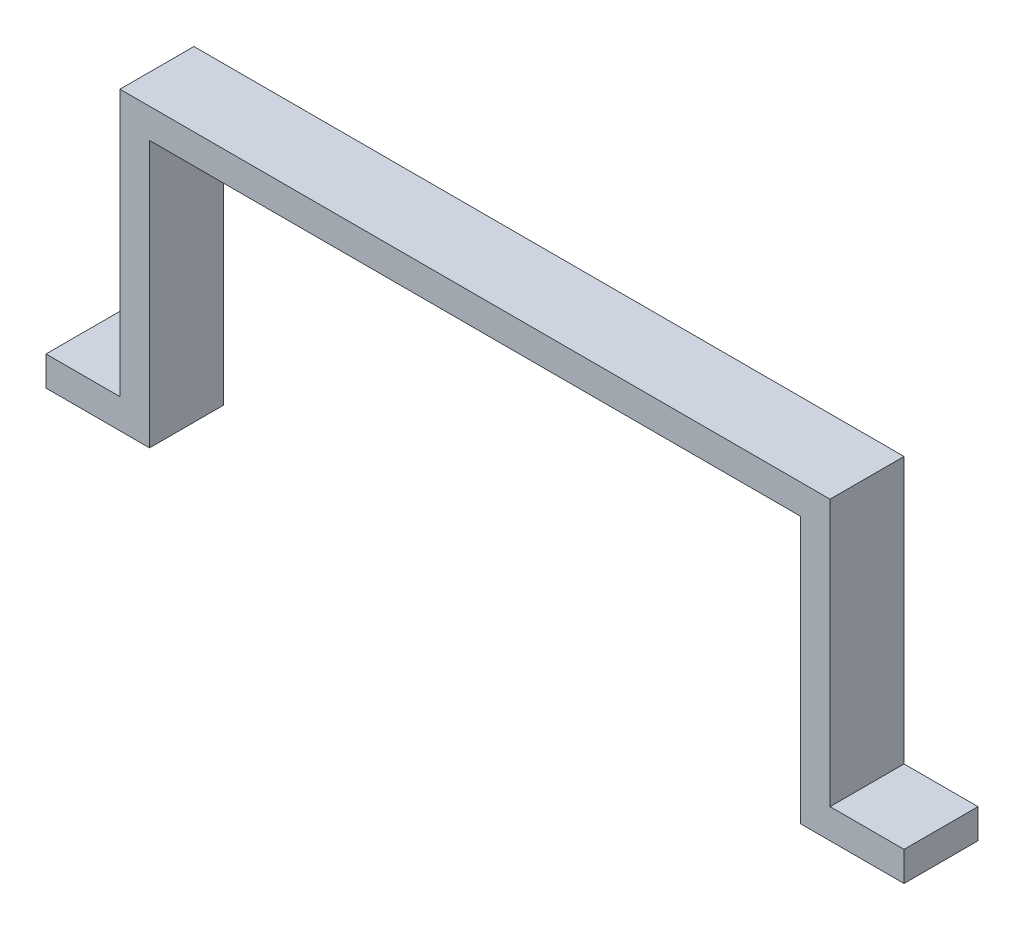
SolidWorks part; units mm, degrees
ref_plane "Front Plane" through (0, 0, 0) normal (0, 0, 1) x (1, 0, 0)
ref_plane "Top Plane" through (0, 0, 0) normal (0, 1, 0) x (1, 0, 0)
ref_plane "Right Plane" through (0, 0, 0) normal (1, 0, 0) x (0, 0, -1)
sketch "Sketch1" plane through (0, 0, 0) normal (0, 0, 1) x (1, 0, 0)
  line L0 (-290, 0) -> (-220, 0)
  line L1 (240, 140.36) -> (240, 20)
  line L2 (240, 200) -> (240, 140.36)
  line L3 (-270, 20) -> (-240, 20)
  line L4 (-220, 20) -> (-220, 180)
  line L5 (-220, 180) -> (220, 180)
  line L6 (-220, 20) -> (-220, 0)
  line L8 (240, 200) -> (-240, 200)
  line L9 (-240, 200) -> (-240, 140.36)
  line L10 (-240, 140.36) -> (-240, 20)
  line L11 (-240, 20) -> (-290, 20)
  line L12 (-290, 20) -> (-290, 0)
  line L13 (220, 20) -> (220, 180)
  line L14 (220, 20) -> (220, 0)
  line L15 (290, 0) -> (220, 0)
  line L16 (290, 20) -> (290, 0)
  line L17 (240, 20) -> (290, 20)
  line L18 (-240, 20) -> (-240, 106.3138)
  dimension "D6" = 20
  dimension "D7" = 50
extrude "Boss-Extrude1" add sketch "Sketch1" along normal blind 50 contours L11 L12 L0 L6 L4 L5 L13 L14 L15 L16 L17 L1 L2 L8 L9 L10
